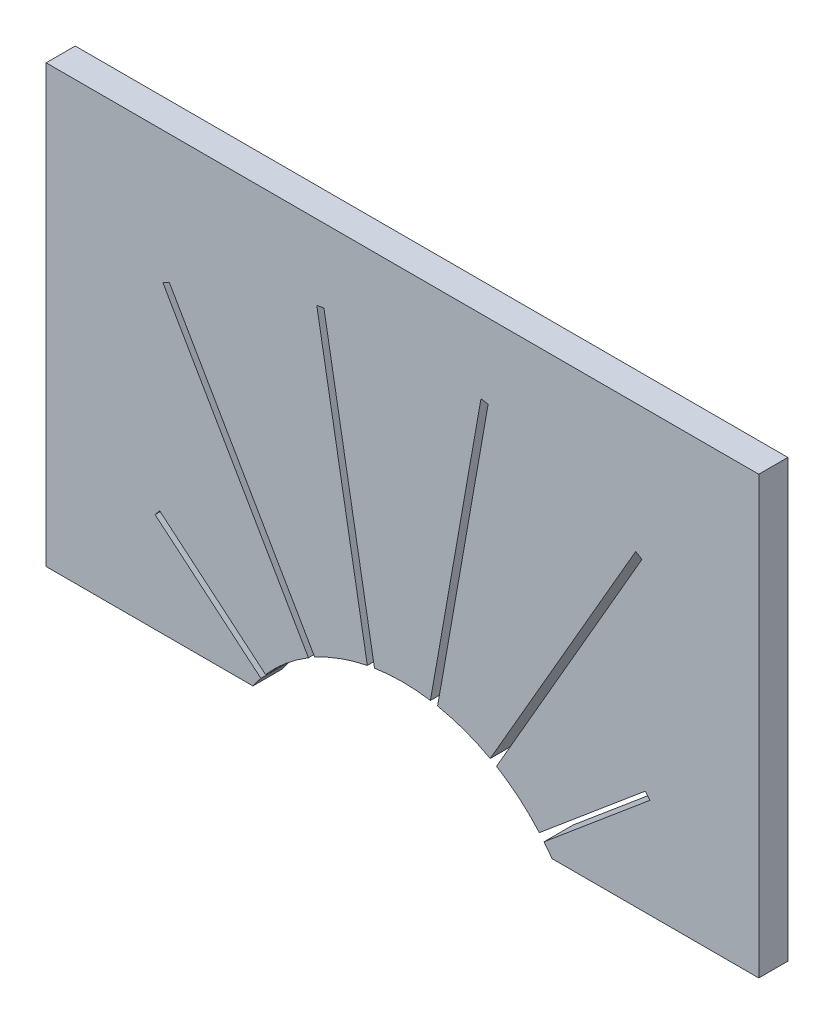
SolidWorks part; units mm, degrees
material "Rubber"
ref_plane "Front Plane" through (0, 0, 0) normal (0, 0, 1) x (1, 0, 0)
ref_plane "Top Plane" through (0, 0, 0) normal (0, 1, 0) x (1, 0, 0)
ref_plane "Right Plane" through (0, 0, 0) normal (1, 0, 0) x (0, 0, -1)
sketch "Sketch1" plane through (0, 0, 0) normal (0, 0, 1) x (1, 0, 0)
  line L1 (-24.5, -15) -> (24.5, -15)
  line L2 (-24.5, -15) -> (-24.5, 15)
  line L3 (-24.5, 15) -> (24.5, 15)
  line L4 (24.5, -15) -> (24.5, 15)
  line L5 (-24.5, -15) -> (24.5, 15) construction
  line L6 (-24.5, 15) -> (24.5, -15) construction
  point P0 (0, 0)
  dimension "D1" = 49
  dimension "D2" = 30
extrude "Boss-Extrude1" add sketch "Sketch1" along normal mid plane 2
sketch "Sketch2" plane through (0, 0, 1) normal (0, 0, 1) x (1, 0, 0)
  line L0 (0, -22.112) -> (-16.853, -7.9707) construction
  line L1 (0, -22.112) -> (-16.255, 6.0425) construction
  line L2 (0, -22.112) -> (-5.6453, 9.9041) construction
  line L3 (0, -22.112) -> (0, 10.398) construction
  line L4 (-0.2166, -22.2368) -> (-0.9254, -21.0091) construction
  line L5 (-9.7343, -14.2703) -> (-17.0137, -8.1622)
  line L6 (-0.2462, -22.1555) -> (-0.4924, -20.7591) construction
  line L7 (0.2164, -21.9868) -> (-0.4924, -20.7591) construction
  line L8 (0.1607, -21.9205) -> (-0.9254, -21.0091) construction
  line L9 (0.2462, -22.0684) -> (0, -20.6723) construction
  line L10 (0.2165, -21.987) -> (-16.0385, 6.1675) construction
  line L11 (-0.2165, -22.237) -> (-16.4715, 5.9175) construction
  line L12 (-0.2462, -22.1554) -> (-5.8915, 9.8607) construction
  line L13 (0.2462, -22.0686) -> (-5.3991, 9.9475) construction
  line L14 (-17.0137, -8.1622) -> (-16.6923, -7.7792)
  line L15 (-9.4129, -13.8873) -> (-16.6923, -7.7792)
  line L16 (-0.1607, -22.3035) -> (-17.0137, -8.1622) construction
  line L17 (-6.4653, -11.4138) -> (-16.471, 5.9167)
  line L18 (0.1607, -21.9205) -> (-16.6923, -7.7792) construction
  line L19 (-6.0322, -11.1638) -> (-16.038, 6.1667)
  line L20 (-2.4164, -9.8478) -> (-5.8913, 9.8597)
  line L21 (-1.924, -9.761) -> (-5.3989, 9.9466)
  line L22 (1.924, -9.761) -> (5.3989, 9.9466)
  line L23 (2.4164, -9.8478) -> (5.8913, 9.8597)
  line L24 (6.0322, -11.1638) -> (16.038, 6.1667)
  line L25 (6.4653, -11.4138) -> (16.471, 5.9167)
  line L26 (9.4129, -13.8873) -> (16.6923, -7.7792)
  line L27 (17.0137, -8.1622) -> (16.6923, -7.7792)
  line L28 (9.7343, -14.2703) -> (17.0137, -8.1622)
  line L29 (-10.2796, -15) -> (10.2796, -15)
  line L30 (-24.5, -15) -> (24.5, -15) construction
  arc A0 (-16.038, 6.1667) -> (-16.471, 5.9167) centre (0, -22.112) ccw
  arc A1 (10.2796, -15) -> (9.7343, -14.2703) centre (0, -22.112) ccw
  arc A2 (16.471, 5.9167) -> (16.038, 6.1667) centre (0, -22.112) ccw
  arc A3 (5.8913, 9.8597) -> (5.3989, 9.9466) centre (0, -22.112) ccw
  arc A4 (-5.3989, 9.9466) -> (-5.8913, 9.8597) centre (0, -22.112) ccw
  arc A5 (-6.4653, -11.4138) -> (-9.4129, -13.8873) centre (0, -22.112) ccw
  arc A6 (-9.7343, -14.2703) -> (-10.2796, -15) centre (0, -22.112) ccw
  arc A7 (-2.4164, -9.8478) -> (-6.0322, -11.1638) centre (0, -22.112) ccw
  arc A8 (1.924, -9.761) -> (-1.924, -9.761) centre (0, -22.112) ccw
  arc A9 (6.0322, -11.1638) -> (2.4164, -9.8478) centre (0, -22.112) ccw
  arc A10 (9.4129, -13.8873) -> (6.4653, -11.4138) centre (0, -22.112) ccw
  dimension "D2" = 65.02
  dimension "D5" = 25
  dimension "D1" = 22.112
  dimension "D6" = 20
  dimension "D7" = 10
  dimension "D8" = 20
  dimension "D9" = 22
  dimension "D3" = 0.25
  dimension "D4" = 0.25
extrude "Cut-Extrude1" cut sketch "Sketch2" against normal blind 10
